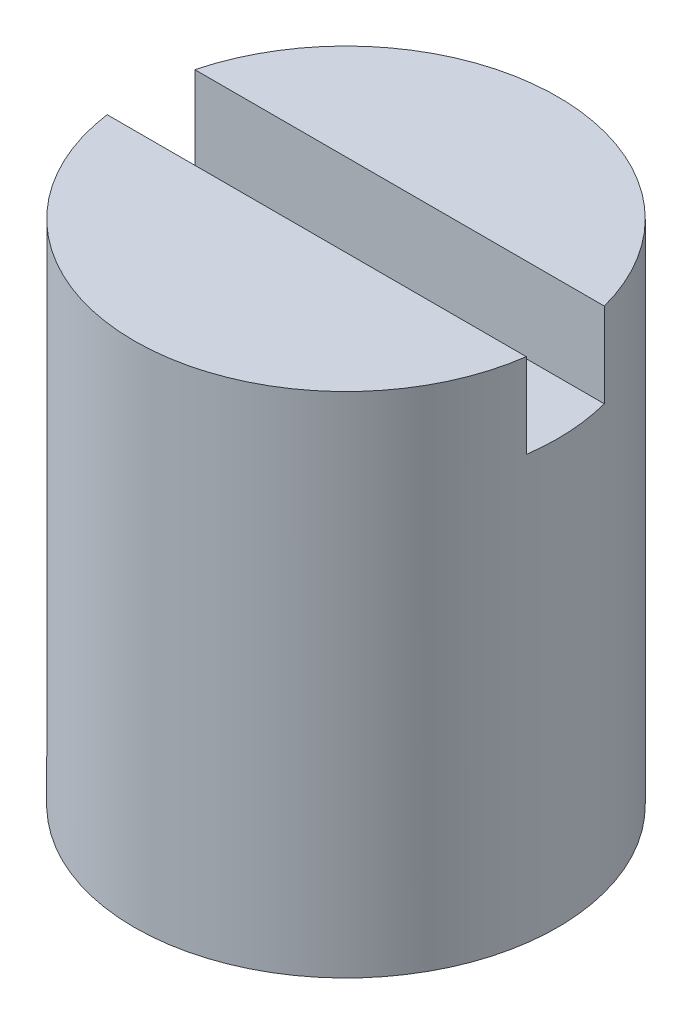
SolidWorks part; units mm, degrees
ref_plane "Front Plane" through (0, 0, 0) normal (0, 0, 1) x (1, 0, 0)
ref_plane "Top Plane" through (0, 0, 0) normal (0, 1, 0) x (1, 0, 0)
ref_plane "Right Plane" through (0, 0, 0) normal (1, 0, 0) x (0, 0, -1)
sketch "Sketch1" plane through (0, 0, 0) normal (0, 1, 0) x (1, 0, 0)
  circle A0 centre (0, 0) radius 7.5
  dimension "D1" = 15
extrude "Boss-Extrude1" add sketch "Sketch1" along normal blind 18
sketch "Sketch2" plane through (0, 18, 0) normal (0, 1, 0) x (1, 0, 0)
  line L1 (-12.6811, 1.8991) -> (11.4831, 1.8991)
  line L2 (-12.6811, 1.8991) -> (-12.6811, -1.0368)
  line L3 (-12.6811, -1.0368) -> (11.4831, -1.0368)
  line L4 (11.4831, 1.8991) -> (11.4831, -1.0368)
extrude "Cut-Extrude1" cut sketch "Sketch2" against normal blind 3
